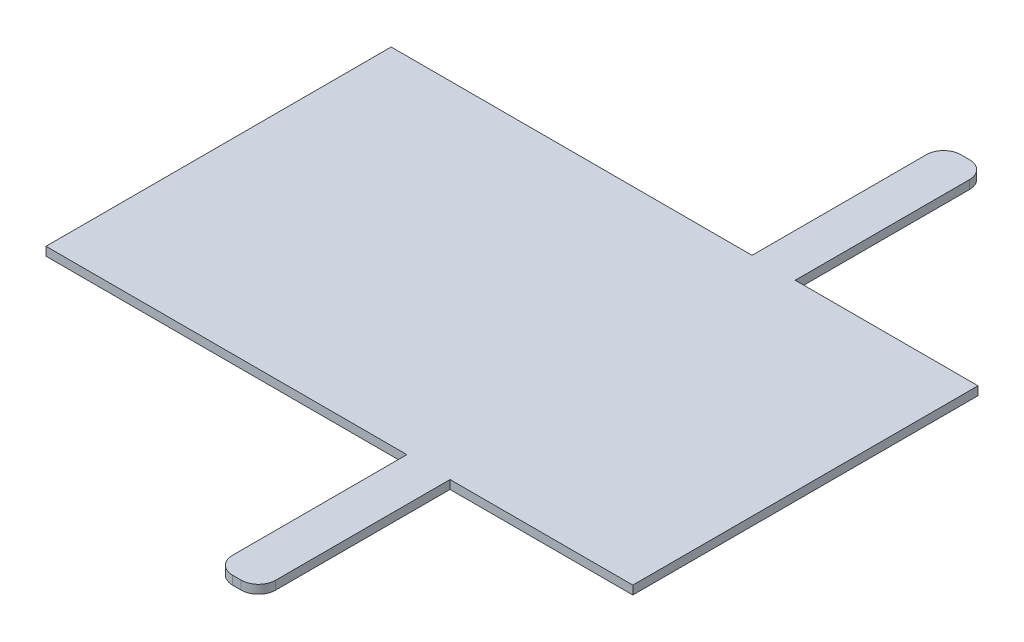
SolidWorks part; units mm, degrees
ref_plane "Front" through (0, 0, 0) normal (0, 0, 1) x (1, 0, 0)
ref_plane "Top" through (0, 0, 0) normal (0, 1, 0) x (1, 0, 0)
ref_plane "Right" through (0, 0, 0) normal (1, 0, 0) x (0, 0, -1)
sketch "Sketch1" plane through (0, 0, 0) normal (0, 1, 0) x (1, 0, 0)
  line L0 (-457.2086, 422.6316) -> (-351.2965, 422.6316)
  line L1 (-691.2965, 422.6316) -> (-482.2086, 422.6316)
  line L2 (-691.2965, 422.6316) -> (-691.2965, 222.6316)
  line L3 (-691.2965, 222.6316) -> (-482.2086, 222.6316)
  line L4 (-351.2965, 422.6316) -> (-351.2965, 222.6316)
  line L6 (-482.2086, 422.6316) -> (-482.2086, 523.6316)
  line L7 (-472.2086, 533.6316) -> (-467.2086, 533.6316)
  line L8 (-457.2086, 422.6316) -> (-457.2086, 523.6316)
  line L9 (-351.2965, 322.6316) -> (-691.2965, 322.6316) construction
  line L10 (-457.2086, 222.6316) -> (-457.2086, 121.6316)
  line L11 (-472.2086, 111.6316) -> (-467.2086, 111.6316)
  line L12 (-482.2086, 222.6316) -> (-482.2086, 121.6316)
  line L13 (-457.2086, 222.6316) -> (-351.2965, 222.6316)
  arc A0 (-467.2086, 533.6316) -> (-457.2086, 523.6316) centre (-467.2086, 523.6316) cw
  arc A1 (-482.2086, 523.6316) -> (-472.2086, 533.6316) centre (-472.2086, 523.6316) cw
  arc A2 (-482.2086, 121.6316) -> (-472.2086, 111.6316) centre (-472.2086, 121.6316) ccw
  arc A3 (-467.2086, 111.6316) -> (-457.2086, 121.6316) centre (-467.2086, 121.6316) ccw
  point P10 (-457.2086, 533.6316)
  point P13 (-482.2086, 533.6316)
  point P24 (-482.2086, 111.6316)
  point P25 (-457.2086, 111.6316)
  dimension "D5" = 10
  dimension "D1" = 340
  dimension "D2" = 200
  dimension "D3" = 25
  dimension "D4" = 111
extrude "Boss-Extrude1" add sketch "Sketch1" along normal blind 5
